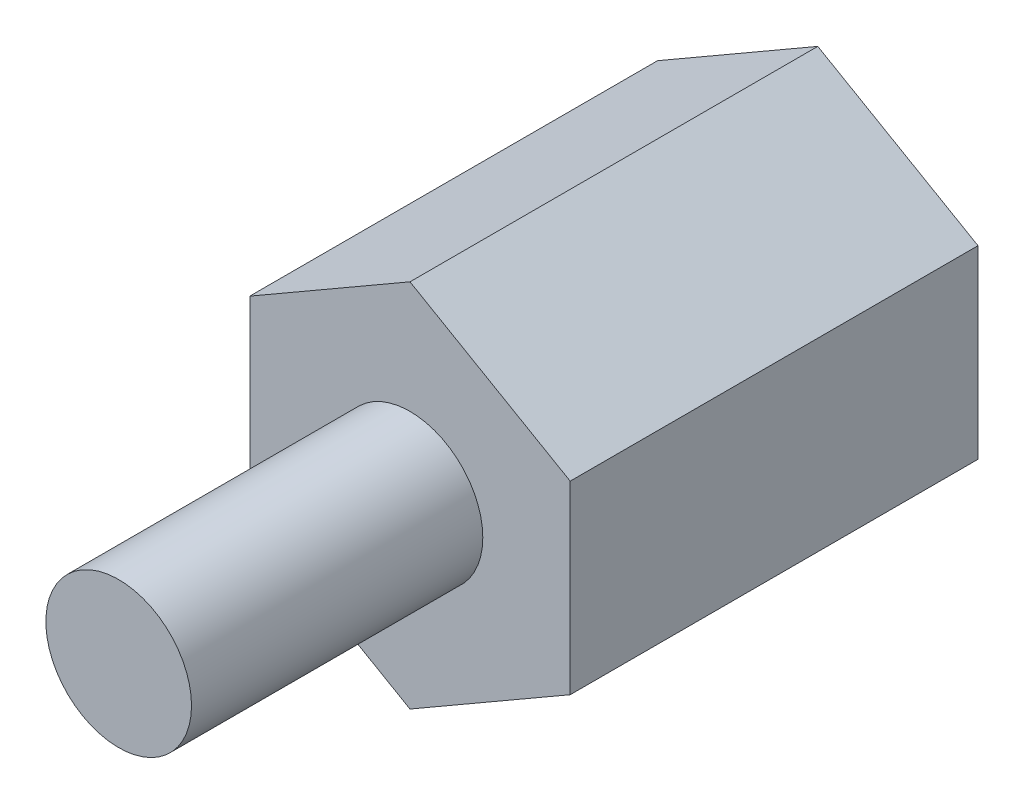
SolidWorks part; units mm, degrees
ref_plane "Front Plane" through (0, 0, 0) normal (0, 0, 1) x (1, 0, 0)
ref_plane "Top Plane" through (0, 0, 0) normal (0, 1, 0) x (1, 0, 0)
ref_plane "Right Plane" through (0, 0, 0) normal (1, 0, 0) x (0, 0, -1)
ref_plane "Plane1"
sketch "Sketch1" plane through (0, 0, 0) normal (0, 0, 1) x (1, 0, 0)
  line L0 (0, 3.1754) -> (-2.75, 1.5877)
  line L1 (-2.75, 1.5877) -> (-2.75, -1.5877)
  line L2 (-2.75, -1.5877) -> (0, -3.1754)
  line L3 (0, -3.1754) -> (2.75, -1.5877)
  line L4 (2.75, -1.5877) -> (2.75, 1.5877)
  line L5 (2.75, 1.5877) -> (0, 3.1754)
  dimension "D1" = 5.5
extrude "Extrusion1" add sketch "Sketch1" along normal blind 6 and the other way blind 6
sketch "Sketch2" plane through (0, 0, -6) normal (0, 0, -1) x (-1, 0, 0)
  circle A0 centre (0, 0) radius 1.25
  dimension "D1" = 2.5
extrude "Extrusion2" cut sketch "Sketch2" against normal blind 4
sketch "Sketch3" plane through (0, 0, 6) normal (0, 0, 1) x (1, 0, 0)
  line L0 (2.75, 1.5877) -> (0, 3.1754)
  line L1 (0, 3.1754) -> (-2.75, 1.5877)
  line L2 (-2.75, 1.5877) -> (-2.75, -1.5877)
  line L3 (-2.75, -1.5877) -> (0, -3.1754)
  line L4 (0, -3.1754) -> (2.75, -1.5877)
  line L5 (2.75, -1.5877) -> (2.75, 1.5877)
  circle A0 centre (0, 0) radius 1.25
  line M1 (2.75, 1.5877) -> (0, 3.1754)
  line M2 (0, 3.1754) -> (-2.75, 1.5877)
  line M3 (-2.75, 1.5877) -> (-2.75, -1.5877)
  line M4 (-2.75, -1.5877) -> (0, -3.1754)
  line M5 (0, -3.1754) -> (2.75, -1.5877)
  line M6 (2.75, -1.5877) -> (2.75, 1.5877)
  dimension "D1" = 2.5
extrude "Thread2" cut sketch "Sketch3" against normal blind 5 contours A0 M6 M1 M2 M3 M4 M5
cosmetic thread "Cosmetic Thread2" parameters "D2"=2.439
